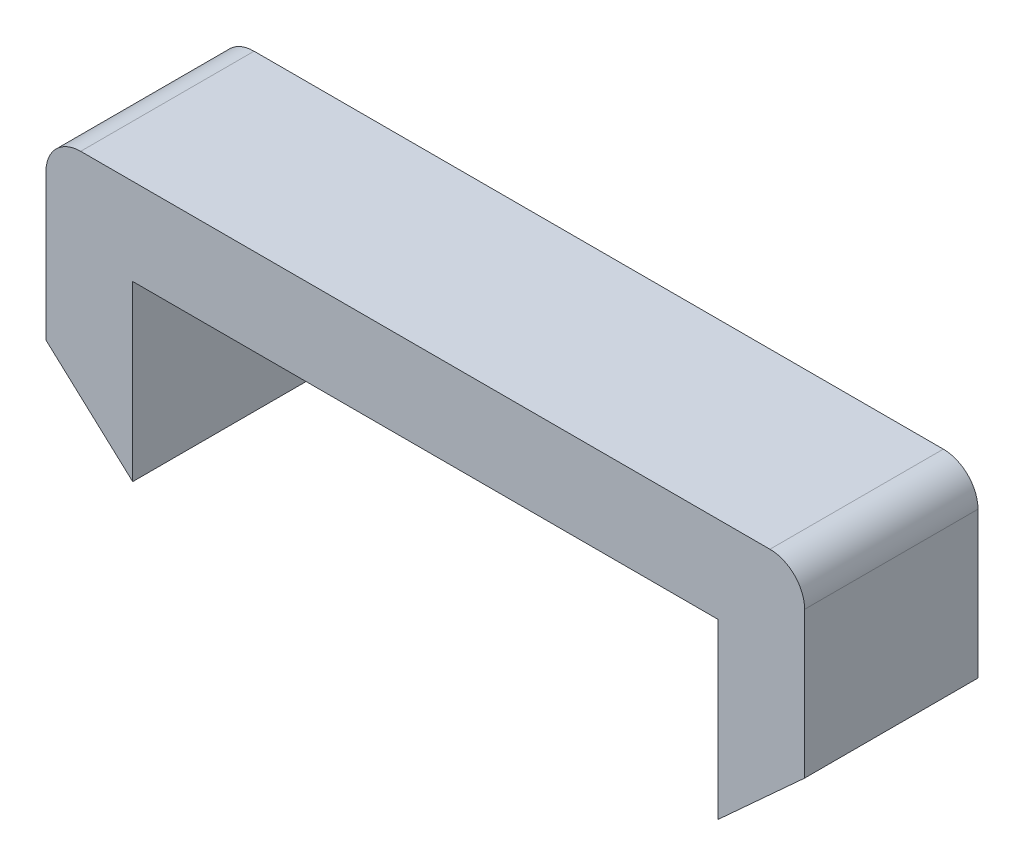
SolidWorks part; units mm, degrees
ref_plane "前视基准面" through (0, 0, 0) normal (0, 0, 1) x (1, 0, 0)
ref_plane "上视基准面" through (0, 0, 0) normal (0, 1, 0) x (1, 0, 0)
ref_plane "右视基准面" through (0, 0, 0) normal (1, 0, 0) x (0, 0, -1)
other "Configuration Table"
sketch "草图1" plane through (0, 0, 0) normal (0, 0, 1) x (1, 0, 0)
  line L0 (-26.9539, 1.1516) -> (-21.9539, 1.1516)
  line L1 (-21.9539, 1.1516) -> (-21.9539, 11.1516)
  line L2 (-21.9539, 11.1516) -> (11.7961, 11.1516)
  line L3 (11.7961, 11.1516) -> (11.7961, 1.1516)
  line L4 (11.7961, 1.1516) -> (16.7961, 1.1516)
  line L5 (16.7961, 1.1516) -> (16.7961, 16.1516)
  line L6 (16.7961, 16.1516) -> (-26.9539, 16.1516)
  line L7 (-26.9539, 16.1516) -> (-26.9539, 1.1516)
  dimension "D1" = 33.75
  dimension "D2" = 10
  dimension "D3" = 10
  dimension "D4" = 5
  dimension "D5" = 5
  dimension "D6" = 5
extrude "凸台-拉伸1" add sketch "草图1" along normal blind 10
fillet "圆角1" radius 2 2 edges at (16.7961, 16.1516, 5) (-26.9539, 16.1516, 5)
sketch "草图2" plane through (0, 0, 10) normal (0, 0, 1) x (1, 0, 0)
  line L0 (-26.9539, 1.1516) -> (-21.9539, 1.1516)
  line L3 (-26.9539, 14.1516) -> (-26.9539, 1.1516) construction
  line L4 (-26.9539, 5.7182) -> (-21.9539, 1.1516)
  line L5 (-26.9539, 5.7182) -> (-26.9539, 1.1516)
extrude "切除-拉伸1" cut sketch "草图2" against normal through all
sketch "草图3" plane through (0, 0, 10) normal (0, 0, 1) x (1, 0, 0)
  line L1 (16.7961, 1.1516) -> (16.7961, 14.1516) construction
  line L2 (16.7961, 5.7182) -> (11.7961, 1.1516)
  line L3 (11.7961, 1.1516) -> (16.7961, 1.1516)
  line L4 (11.7961, 1.1516) -> (16.7961, 1.1516) construction
  line L5 (16.7961, 1.1516) -> (16.7961, 5.7182)
extrude "切除-拉伸2" cut sketch "草图3" against normal through all
